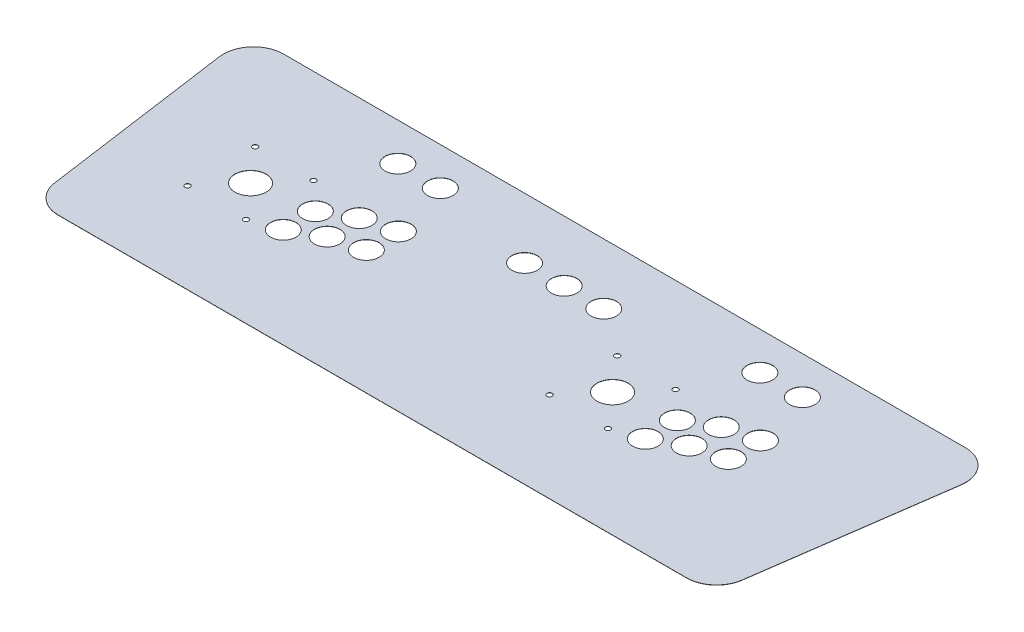
SolidWorks part; units mm, degrees
ref_plane "Front Plane" through (0, 0, 0) normal (0, 0, 1) x (1, 0, 0)
ref_plane "Top Plane" through (0, 0, 0) normal (0, 1, 0) x (1, 0, 0)
ref_plane "Right Plane" through (0, 0, 0) normal (1, 0, 0) x (0, 0, -1)
sketch "Sketch1" plane through (0, 0, 0) normal (0, 1, 0) x (1, 0, 0)
  line L9 (335.7562, 149.733) -> (-335.7563, 149.733)
  line L10 (335.7562, 149.733) -> (335.7562, -149.733)
  line L11 (335.7562, -149.733) -> (-335.7562, -149.733)
  line L12 (-335.7563, 149.733) -> (-335.7562, -149.733)
  line L13 (335.7562, 149.733) -> (-335.7562, -149.733) construction
  line L14 (335.7562, -149.733) -> (-335.7563, 149.733) construction
  point P0 (0, 0)
  dimension "D1" = 299.466
  dimension "D2" = 671.5125
extrude "Boss-Extrude1" add sketch "Sketch1" along normal mid plane 0.2032
sketch "Sketch2" plane through (0, 0.1016, 0) normal (0, 1, 0) x (1, 0, 0)
  line L0 (335.7562, -149.733) -> (374.6439, -149.733)
  line L1 (374.6439, -149.733) -> (412.0832, 116.6621)
  line L2 (412.0832, 116.6621) -> (335.7562, 116.6621)
  line L3 (335.7562, -149.733) -> (335.7562, 149.733) construction
  line L4 (335.7562, 116.6621) -> (335.7562, -149.733)
  line L5 (412.0832, 116.6621) -> (412.0833, -148.5139) construction
  line L6 (0, 0) -> (0, 149.733) construction
  line L7 (335.7562, 149.733) -> (-335.7563, 149.733) construction
  line L8 (-412.0832, 116.6621) -> (-412.0833, -148.5139) construction
  line L9 (-335.7562, 116.6621) -> (-335.7562, -149.733)
  line L10 (-412.0832, 116.6621) -> (-335.7562, 116.6621)
  line L11 (-374.6439, -149.733) -> (-412.0832, 116.6621)
  line L12 (-335.7562, -149.733) -> (-374.6439, -149.733)
  dimension "D1" = 266.3951
  dimension "D2" = 76.327
  dimension "D3" = 8
  dimension "D4" = 824.1665
extrude "Boss-Extrude2" add sketch "Sketch2" against normal up to surface (0.2032 mm away) up to face at (0, -0.1016, 0)
fillet "Fillet1" radius 25.4 4 edges at (-412.0832, 0, -116.6621) (-374.6439, 0, 149.733) (412.0832, 0, -116.6621) (374.6439, 0, 149.733)
sketch "Sketch3" plane through (0, 0.1016, 0) normal (0, 1, 0) x (1, 0, 0)
  line L0 (-212.087, -46.05) -> (-212.087, -10.05) construction
  line L1 (-180.837, -28.05) -> (-180.837, 7.95) construction
  line L2 (-145.837, -19.05) -> (-145.837, 16.95) construction
  line L3 (-145.837, -19.05) -> (-145.837, -46.05) construction
  line L4 (-180.837, -28.05) -> (-180.837, -46.05) construction
  line L5 (-212.087, -46.05) -> (-180.837, -46.05) construction
  line L6 (-275.837, -19.05) -> (130.563, -19.05) construction
  line L7 (-180.837, -46.05) -> (-145.837, -46.05) construction
  line L8 (-212.087, 82.55) -> (-164.3697, 82.55) construction
  line L9 (-275.837, -19.05) -> (-275.837, 82.55) construction
  line L10 (-145.837, -46.05) -> (-112.0113, -46.05) construction
  line L11 (-212.087, -46.05) -> (-275.837, -46.05) construction
  line L12 (-275.837, 82.55) -> (-212.087, 82.55) construction
  line L13 (-275.837, -19.05) -> (-275.837, -46.05) construction
  line L14 (194.313, -46.05) -> (194.313, -10.05) construction
  line L15 (225.563, -28.05) -> (225.563, 7.95) construction
  line L16 (260.563, -19.05) -> (260.563, 16.95) construction
  line L17 (260.563, -19.05) -> (260.563, -46.05) construction
  line L18 (225.563, -28.05) -> (225.563, -46.05) construction
  line L19 (194.313, -46.05) -> (225.563, -46.05) construction
  line L20 (225.563, -46.05) -> (260.563, -46.05) construction
  line L21 (194.313, 82.55) -> (242.0303, 82.55) construction
  line L22 (130.563, -19.05) -> (130.563, 82.55) construction
  line L23 (194.313, -46.05) -> (130.563, -46.05) construction
  line L24 (130.563, 82.55) -> (194.313, 82.55) construction
  line L25 (130.563, -19.05) -> (130.563, -46.05) construction
  line L26 (-44.45, 57.15) -> (44.45, 57.15) construction
  line L27 (-275.837, -19.05) -> (-275.837, -71.5396) construction
  line L28 (-275.837, -71.5396) -> (-114.1857, -71.5396) construction
  line L29 (-114.1857, -71.5396) -> (-114.1857, -19.05) construction
  line L30 (130.563, -19.05) -> (130.563, -71.5396) construction
  line L31 (130.563, -71.5396) -> (259.4596, -71.5396) construction
  line L32 (-195.0113, -71.5396) -> (-195.0113, -17.7133) construction
  line L33 (195.0113, -71.5396) -> (195.0113, -17.7133) construction
  line L34 (0, -80.6856) -> (0, 57.15) construction
  line L36 (-243.037, 18.9) -> (-308.637, 18.9) construction
  line L37 (-243.037, 18.9) -> (-243.037, -57) construction
  line L38 (-243.037, -57) -> (-308.637, -57) construction
  line L39 (-308.637, 18.9) -> (-308.637, -57) construction
  line L40 (-243.037, 18.9) -> (-308.637, -57) construction
  line L41 (-243.037, -57) -> (-308.637, 18.9) construction
  line L42 (163.363, 18.9) -> (97.763, 18.9) construction
  line L43 (163.363, 18.9) -> (163.363, -57) construction
  line L44 (163.363, -57) -> (97.763, -57) construction
  line L45 (97.763, 18.9) -> (97.763, -57) construction
  line L46 (163.363, 18.9) -> (97.763, -57) construction
  line L47 (163.363, -57) -> (97.763, 18.9) construction
  circle A0 centre (-275.837, -19.05) radius 17.5
  circle A1 centre (-180.837, 7.95) radius 14.2875
  circle A2 centre (-145.837, 16.95) radius 14.2875
  circle A3 centre (-145.837, -19.05) radius 14.2875
  circle A4 centre (-180.837, -28.05) radius 14.2875
  circle A5 centre (-212.087, -10.05) radius 14.2875
  circle A6 centre (-212.087, -46.05) radius 14.2875
  circle A7 centre (-212.087, 82.55) radius 14.2875
  circle A8 centre (-164.3697, 82.55) radius 14.2875
  circle A9 centre (130.563, -19.05) radius 17.5
  circle A10 centre (225.563, 7.95) radius 14.2875
  circle A11 centre (260.563, 16.95) radius 14.2875
  circle A12 centre (260.563, -19.05) radius 14.2875
  circle A13 centre (225.563, -28.05) radius 14.2875
  circle A14 centre (194.313, -10.05) radius 14.2875
  circle A15 centre (194.313, -46.05) radius 14.2875
  circle A16 centre (194.313, 82.55) radius 14.2875
  circle A17 centre (242.0303, 82.55) radius 14.2875
  circle A21 centre (-308.637, 18.9) radius 2.95
  circle A22 centre (-243.037, 18.9) radius 2.95
  circle A23 centre (-308.637, -57) radius 2.95
  circle A24 centre (-243.037, -57) radius 2.95
  circle A25 centre (97.763, 18.9) radius 2.95
  circle A26 centre (163.363, 18.9) radius 2.95
  circle A27 centre (97.763, -57) radius 2.95
  circle A28 centre (163.363, -57) radius 2.95
  circle A30 centre (-44.45, 57.15) radius 14.2875
  circle A32 centre (0, 57.15) radius 14.2875
  circle A33 centre (44.45, 57.15) radius 14.2875
  point P47 (0, 0)
  point P62 (0, 57.15)
  dimension "D1" = 28.575
  dimension "D8" = 35
  dimension "D17" = 5.9
  dimension "D18" = 65.6
  dimension "D13" = 76.2
  dimension "D12" = 44.45
  dimension "D2" = 35
  dimension "D3" = 31.25
  dimension "D4" = 18
  dimension "D5" = 9
  dimension "D6" = 36
  dimension "D7" = 95
  dimension "D9" = 47.7173
  dimension "D10" = 101.6
  dimension "D11" = 63.75
  dimension "D14" = 406.4
  dimension "D15" = 25.4896
  dimension "D19" = 75.9
  dimension "D20" = 19.05
  dimension "D21" = 130.563
extrude "Cut-Extrude1" cut sketch "Sketch3" against normal through all both and the other way through all
sketch "Sketch4" plane through (0, 0.1016, 0) normal (0, 1, 0) x (1, 0, 0)
  line L1 (-335.7563, 116.6621) -> (335.7562, 116.6621)
  line L2 (-335.7563, 116.6621) -> (-335.7563, 149.733)
  line L3 (-335.7563, 149.733) -> (335.7562, 149.733)
  line L4 (335.7562, 116.6621) -> (335.7562, 149.733)
extrude "Cut-Extrude2" cut sketch "Sketch4" against normal through all both and the other way through all
sketch "Sketch5" plane through (0, 0.1016, 0) normal (0, 1, 0) x (1, 0, 0)
  line L0 (382.8639, 124.9679) -> (-382.8639, 124.9679)
  line L1 (-416.2417, 86.5712) -> (-385.9417, -129.0239)
  line L2 (-352.564, -158.0388) -> (352.564, -158.0388)
  line L3 (385.9417, -129.0239) -> (416.2417, 86.5712)
  line L4 (382.8639, 116.6621) -> (-382.8639, 116.6621)
  line L5 (-408.0167, 87.7272) -> (-377.7168, -127.868)
  line L6 (-352.564, -149.733) -> (352.564, -149.733)
  line L7 (377.7168, -127.868) -> (408.0167, 87.7272)
  line L8 (382.8639, 116.6621) -> (-382.8639, 116.6621)
  line L9 (-408.0167, 87.7272) -> (-377.7168, -127.868)
  line L10 (-352.564, -149.733) -> (352.564, -149.733)
  line L11 (377.7168, -127.868) -> (408.0167, 87.7272)
  arc A0 (416.2417, 86.5712) -> (382.8639, 124.9679) centre (382.8639, 91.2621) ccw
  arc A1 (-382.8639, 124.9679) -> (-416.2417, 86.5712) centre (-382.8639, 91.2621) ccw
  arc A2 (-385.9417, -129.0239) -> (-352.564, -158.0388) centre (-352.564, -124.333) ccw
  arc A3 (352.564, -158.0388) -> (385.9417, -129.0239) centre (352.564, -124.333) ccw
  arc A4 (408.0167, 87.7272) -> (382.8639, 116.6621) centre (382.8639, 91.2621) ccw
  arc A5 (-382.8639, 116.6621) -> (-408.0167, 87.7272) centre (-382.8639, 91.2621) ccw
  arc A6 (-377.7168, -127.868) -> (-352.564, -149.733) centre (-352.564, -124.333) ccw
  arc A7 (352.564, -149.733) -> (377.7168, -127.868) centre (352.564, -124.333) ccw
  arc A8 (408.0167, 87.7272) -> (382.8639, 116.6621) centre (382.8639, 91.2621) ccw
  arc A9 (-382.8639, 116.6621) -> (-408.0167, 87.7272) centre (-382.8639, 91.2621) ccw
  arc A10 (-377.7168, -127.868) -> (-352.564, -149.733) centre (-352.564, -124.333) ccw
  arc A11 (352.564, -149.733) -> (377.7168, -127.868) centre (352.564, -124.333) ccw
  dimension "D1" = 0
  dimension "D2" = 8.3058
extrude "Boss-Extrude3" add sketch "Sketch5" against normal up to surface (0.2032 mm away) up to face at (0, -0.1016, 18.0456)
